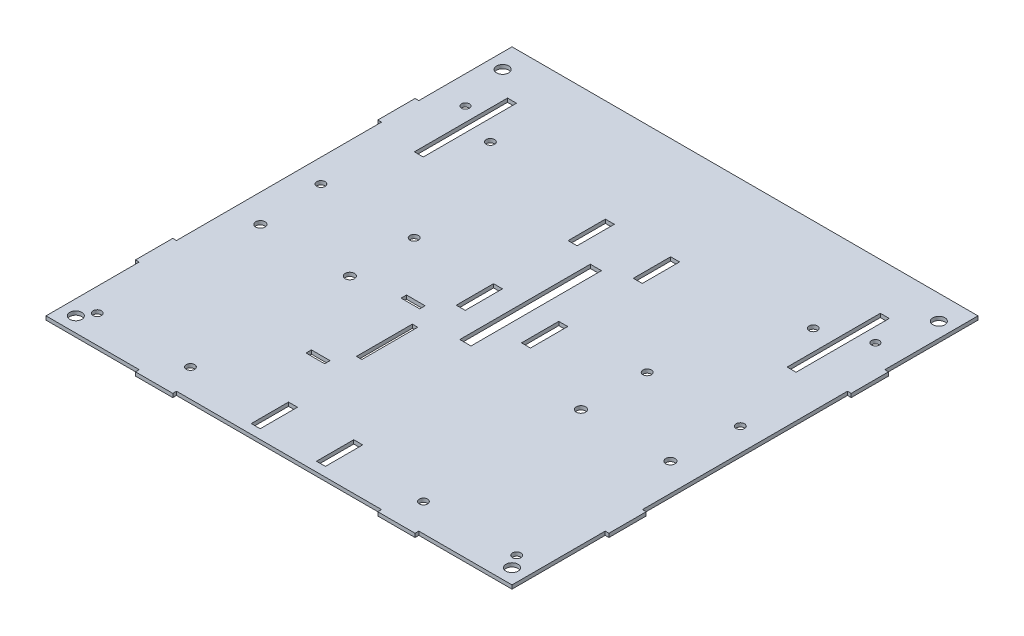
SolidWorks part; units mm, degrees
ref_plane "Front Plane" through (0, 0, 0) normal (0, 0, 1) x (1, 0, 0)
ref_plane "Top Plane" through (0, 0, 0) normal (0, 1, 0) x (1, 0, 0)
ref_plane "Right Plane" through (0, 0, 0) normal (1, 0, 0) x (0, 0, -1)
sketch "Sketch1" plane through (0, 0, 0) normal (0, 1, 0) x (1, 0, 0)
  line L0 (144.9, 25) -> (144.9, 5)
  line L1 (144.9, 5) -> (140.1, 5)
  line L2 (140.1, 25) -> (144.9, 25)
  line L3 (140.1, 5) -> (140.1, 25)
  line L4 (109.9, 5) -> (109.9, 25)
  line L5 (109.9, 25) -> (105.1, 25)
  line L6 (105.1, 25) -> (105.1, 5)
  line L7 (105.1, 5) -> (109.9, 5)
  line L8 (87, 52.4842) -> (97, 52.4842)
  line L9 (97, 55.3842) -> (97, 52.4842)
  line L10 (87, 55.3842) -> (97, 55.3842)
  line L11 (87, 52.4842) -> (87, 55.3842)
  line L12 (105, 64.4342) -> (102.1, 64.4342)
  line L13 (105, 64.4342) -> (105, 94.4342)
  line L14 (102.1, 94.4342) -> (102.1, 64.4342)
  line L15 (102.1, 94.4342) -> (105, 94.4342)
  line L16 (97, 106.3842) -> (97, 103.4842)
  line L17 (97, 106.3842) -> (87, 106.3842)
  line L18 (87, 103.4842) -> (97, 103.4842)
  line L19 (87, 103.4842) -> (87, 106.3842)
  line L20 (109.9, 135) -> (105.1, 135)
  line L21 (109.9, 115) -> (109.9, 135)
  line L22 (105.1, 135) -> (105.1, 115)
  line L23 (105.1, 115) -> (109.9, 115)
  line L24 (144.9, 115) -> (140.1, 115)
  line L25 (140.1, 115) -> (140.1, 135)
  line L26 (144.9, 135) -> (144.9, 115)
  line L27 (140.1, 135) -> (144.9, 135)
  line L28 (227.4, 175) -> (227.4, 225)
  line L29 (222.6, 175) -> (222.6, 225)
  line L30 (227.4, 225) -> (222.6, 225)
  line L31 (222.6, 175) -> (227.4, 175)
  line L32 (125, 100) -> (125, 170) construction
  line L33 (122, 170) -> (128, 170)
  line L34 (122, 170) -> (122, 100)
  line L35 (122, 100) -> (128, 100)
  line L36 (22.6, 225) -> (27.4, 225)
  line L37 (27.4, 225) -> (27.4, 175)
  line L38 (22.6, 175) -> (22.6, 225)
  line L39 (27.4, 175) -> (22.6, 175)
  line L40 (250, 250) -> (0, 250)
  line L41 (0, 250) -> (0, 0)
  line L42 (0, 0) -> (250, 0)
  line L43 (250, 0) -> (250, 250)
  line L44 (128, 170) -> (128, 100)
  dimension "D2" = 22.6
  dimension "D3" = 5.1
  dimension "D4" = 10
  dimension "D5" = 102.1
  dimension "D6" = 2.9
  dimension "D7" = 27.4
  dimension "D8" = 105.1
  dimension "D9" = 4.8
  dimension "D10" = 140.1
  dimension "D11" = 222.6
  dimension "D12" = 5
  dimension "D13" = 25
  dimension "D14" = 52.4842
  dimension "D15" = 250
  dimension "D16" = 64.4342
  dimension "D17" = 103.4842
  dimension "D18" = 94.4342
  dimension "D19" = 115
  dimension "D20" = 50
  dimension "D21" = 6
  dimension "D22" = 70
  dimension "D23" = 175
  dimension "D24" = 125
  dimension "D25" = 250
  dimension "D26" = 80
extrude "Boss-Extrude1" add sketch "Sketch1" along normal blind 2
sketch "Sketch2" plane through (0, 2, 0) normal (0, 1, 0) x (1, 0, 0)
  line L0 (0, 250) -> (0, 0) construction
  line L1 (0, 0) -> (250, 0) construction
  circle A0 centre (15, 100) radius 2.5
  circle A1 centre (63, 100) radius 2.5
  dimension "D1" = 5
  dimension "D2" = 5
  dimension "D3" = 48
  dimension "D4" = 15
  dimension "D5" = 100
extrude "Cut-Extrude1" cut sketch "Sketch2" against normal through all
sketch "Sketch3" plane through (0, 2, 0) normal (0, 1, 0) x (1, 0, 0)
  line L3 (250, 0) -> (250, 250) construction
  circle A0 centre (8, 8) radius 3.25
  circle A1 centre (8, 237) radius 3.25
  dimension "D1" = 6.5
  dimension "D2" = 242
  dimension "D3" = 212
  dimension "D4" = 17
extrude "Cut-Extrude2" cut sketch "Sketch3" against normal through all
ref_plane "Plane1" through (125, 0, 0) normal (-1, 0, 0) x (0, 0, 1)
mirror "Mirror1" about plane through (125, 0, 0) normal (-1, 0, 0) of "Cut-Extrude2"
sketch "Sketch4" plane through (0, 2, 0) normal (0, 1, 0) x (1, 0, 0)
  line L1 (0, 200) -> (-2, 200)
  line L2 (0, 200) -> (0, 180)
  line L3 (0, 180) -> (-2, 180)
  line L4 (-2, 200) -> (-2, 180)
  line L7 (0, 70) -> (-2, 70)
  line L8 (0, 70) -> (0, 50)
  line L9 (0, 50) -> (-2, 50)
  line L10 (-2, 70) -> (-2, 50)
  line L11 (144.9, 5) -> (144.9, 25) construction
  line L12 (50, 0) -> (70, 0)
  line L13 (50, 0) -> (50, -2)
  line L14 (50, -2) -> (70, -2)
  line L15 (70, 0) -> (70, -2)
  line L16 (144.9, 25) -> (140.1, 25) construction
  dimension "D1" = 74.9
  dimension "D2" = 94.9
  dimension "D3" = 144.9
  dimension "D4" = 146.9
  dimension "D5" = 25
  dimension "D6" = 155
  dimension "D7" = 25
extrude "Boss-Extrude2" add sketch "Sketch4" against normal up to vertex (2 mm away)
mirror "Mirror2" about plane through (125, 0, 0) normal (-1, 0, 0) of "Boss-Extrude2"
mirror "Mirror3" about plane through (125, 0, 0) normal (-1, 0, 0) of "Cut-Extrude1"
hole_wizard "Ø4.5 (4.5) Diameter Hole1" positions "Sketch7" profile "Sketch6" hole size "Ø4.5" standard "ISO"
sketch "Sketch7" plane through (0, 2, 0) normal (0, 1, 0) x (1, 0, 0)
  line L0 (252, 200) -> (252, 180) construction
  line L1 (250, 200) -> (252, 200) construction
  point P0 (12.5, 135)
  point P3 (62.5, 135)
  point P6 (62.5, 15)
  point P9 (12.5, 15)
  dimension "D1" = 189.5
  dimension "D2" = 239.5
  dimension "D3" = 65
  dimension "D4" = 185
sketch "Sketch6" plane through (12.5, 2, -135) normal (1, 0, 0) x (0, 0, 1)
  line L0 (0, 0) -> (0, 11.3519)
  line L1 (0, 11.3519) -> (2.25, 10)
  line L2 (2.25, 10) -> (2.25, 0)
  line L5 (2.25, 0) -> (0, 0)
  line L10 (0, 11.3519) -> (-2.25, 10) construction
  line L11 (0, -6.35) -> (0, 107.95) construction
  dimension "Hole Dia." = 4.5
  dimension "Hole Depth" = 10
  dimension "Drill Angle" = 118
mirror "Mirror4" about plane through (125, 0, 0) normal (-1, 0, 0) of "Ø4.5 (4.5) Diameter Hole1"
sketch "Sketch9" plane through (0, 0, 0) normal (0, -1, 0) x (1, 0, 0)
  line L0 (105, -175) -> (110, -175) construction
  line L1 (105.1, -175) -> (109.9, -175)
  line L2 (105.1, -175) -> (105.1, -195)
  line L3 (105.1, -195) -> (109.9, -195)
  line L4 (109.9, -175) -> (109.9, -195)
  line L5 (105, -195) -> (110, -195) construction
  line L6 (105, -175) -> (105, -195) construction
  dimension "D1" = 4.8
  dimension "D2" = 0.1
extrude "Cut-Extrude3" cut sketch "Sketch9" against normal through all
mirror "Mirror5" about plane through (125, 0, 0) normal (-1, 0, 0) of "Cut-Extrude3"
sketch "Sketch10" plane through (0, 0, 0) normal (0, -1, 0) x (1, 0, 0)
  line L0 (0, -250) -> (0, 4.2) construction
  line L1 (250, -250) -> (0, -250) construction
  line L2 (250, -250) -> (250, 4.2) construction
  circle A0 centre (15, -210) radius 2.1
  circle A1 centre (235, -210) radius 2.1
  dimension "D1" = 4.2
  dimension "D2" = 15
  dimension "D3" = 40
  dimension "D4" = 15
extrude "Cut-Extrude4" cut sketch "Sketch10" against normal blind 5
sketch "草图1" plane through (0, 0, 0) normal (0, 1, 0) x (1, 0, 0)
  line L0 (27.4, 175) -> (27.4, 225) construction
  line L1 (250, 250) -> (0, 250) construction
  line L2 (70, 0) -> (180, 0) construction
  line L3 (125, 250) -> (125, 0) construction
  circle A0 centre (38.4, 200) radius 2.25
  circle A1 centre (211.6, 200) radius 2.25
  point P2 (27.4, 200)
  point P3 (125, 0)
  point P6 (125, 250)
  dimension "D1" = 4.5
  dimension "D2" = 11
extrude "切除-拉伸1" cut sketch "草图1" against normal blind 10 and the other way blind 2
